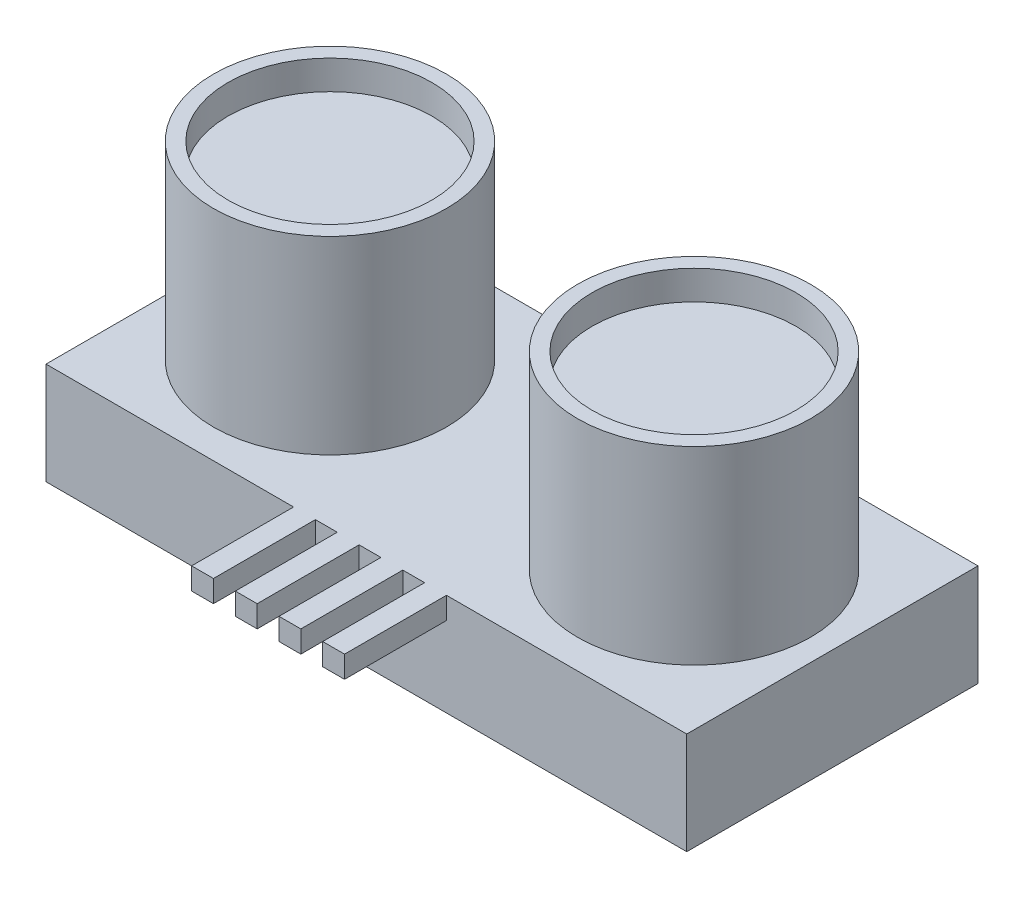
SolidWorks part; units mm, degrees
ref_plane "Front Plane" through (0, 0, 0) normal (0, 0, 1) x (1, 0, 0)
ref_plane "Top Plane" through (0, 0, 0) normal (0, 1, 0) x (1, 0, 0)
ref_plane "Right Plane" through (0, 0, 0) normal (1, 0, 0) x (0, 0, -1)
sketch "Sketch1" plane through (0, 0, 0) normal (0, 1, 0) x (1, 0, 0)
  line L1 (-25.6809, 15.1518) -> (18.3191, 15.1518)
  line L2 (-25.6809, 15.1518) -> (-25.6809, -4.8482)
  line L3 (-25.6809, -4.8482) -> (18.3191, -4.8482)
  line L4 (18.3191, 15.1518) -> (18.3191, -4.8482)
  dimension "D1" = 44
  dimension "D2" = 20
extrude "Boss-Extrude1" add sketch "Sketch1" along normal blind 7
sketch "Sketch3" plane through (0, 7, 0) normal (0, 1, 0) x (1, 0, 0)
  line L0 (-25.6809, 15.1518) -> (-25.6809, -4.8482) construction
  line L1 (18.3191, -4.8482) -> (18.3191, 15.1518) construction
  line L2 (-25.6809, -4.8482) -> (18.3191, -4.8482) construction
  circle A0 centre (-16.1809, 5.1518) radius 8
  circle A1 centre (8.8191, 5.1518) radius 8
  dimension "D1" = 16
  dimension "D2" = 16
  dimension "D3" = 9.5
  dimension "D4" = 9.5
  dimension "D5" = 10
  dimension "D6" = 10
extrude "Boss-Extrude2" add sketch "Sketch3" along normal blind 13
sketch "Sketch4" plane through (0, 20, 0) normal (0, 1, 0) x (1, 0, 0)
  circle A0 centre (-16.1809, 5.1518) radius 7
  circle A1 centre (8.8191, 5.1518) radius 7
  dimension "D1" = 14
  dimension "D2" = 14
extrude "Cut-Extrude1" cut sketch "Sketch4" against normal blind 2
sketch "Sketch5" plane through (0, 0, 4.8482) normal (0, 0, 1) x (1, 0, 0)
  line L0 (-25.6809, 7) -> (18.3191, 7) construction
  line L1 (-8.6809, 7) -> (-7.1809, 7)
  line L2 (-8.6809, 7) -> (-8.6809, 5.5)
  line L3 (-8.6809, 5.5) -> (-7.1809, 5.5)
  line L4 (-7.1809, 7) -> (-7.1809, 5.5)
  line L5 (-5.6809, 5.5) -> (-4.1809, 5.5)
  line L6 (-5.6809, 7) -> (-4.1809, 7)
  line L7 (-5.6809, 7) -> (-5.6809, 5.5)
  line L8 (-4.1809, 7) -> (-4.1809, 5.5)
  line L9 (-2.6809, 5.5) -> (-1.1809, 5.5)
  line L10 (-2.6809, 7) -> (-1.1809, 7)
  line L11 (-2.6809, 7) -> (-2.6809, 5.5)
  line L12 (-1.1809, 7) -> (-1.1809, 5.5)
  line L13 (0.3191, 5.5) -> (1.8191, 5.5)
  line L14 (0.3191, 7) -> (1.8191, 7)
  line L15 (0.3191, 7) -> (0.3191, 5.5)
  line L16 (1.8191, 7) -> (1.8191, 5.5)
  line L17 (-25.6809, 7) -> (-25.6809, 0) construction
  dimension "D1" = 1.5
  dimension "D2" = 1.5
  dimension "D4" = 17
  dimension "D3" = 4
extrude "Boss-Extrude3" add sketch "Sketch5" along normal blind 7
equation "\"ๅถ\"=101.152"
